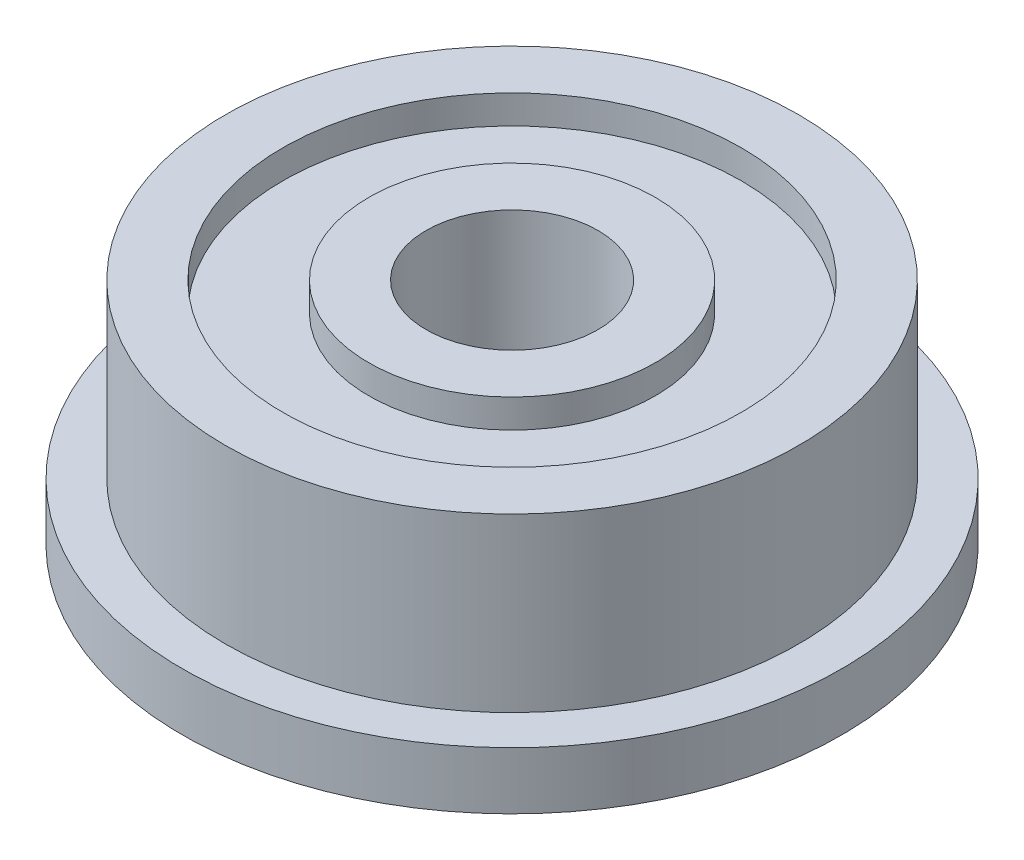
SolidWorks part; units mm, degrees
material "Chrome Stainless Steel"
ref_plane "Front Plane" through (0, 0, 0) normal (0, 0, 1) x (1, 0, 0)
ref_plane "Top Plane" through (0, 0, 0) normal (0, 1, 0) x (1, 0, 0)
ref_plane "Right Plane" through (0, 0, 0) normal (1, 0, 0) x (0, 0, -1)
sketch "Sketch1" plane through (0, 0, 0) normal (0, 0, 1) x (1, 0, 0)
  line L0 (0, -20.7975) -> (0, 26.0194) construction
  line L1 (1.5, 0) -> (1.5, 4)
  line L2 (1.5, 4) -> (2.5, 4)
  line L3 (5, 4) -> (5, 1)
  line L4 (5, 1) -> (5.75, 1)
  line L5 (5.75, 1) -> (5.75, 0)
  line L6 (5.75, 0) -> (4, 0)
  line L7 (4, 4) -> (5, 4)
  line L8 (2.5, 0) -> (1.5, 0)
  line L9 (2.5, 4) -> (2.5, 3.5)
  line L10 (2.5, 3.5) -> (4, 3.5)
  line L11 (4, 4) -> (4, 3.5)
  line L13 (2.5, 0) -> (2.5, 0.5)
  line L14 (2.5, 0.5) -> (4, 0.5)
  line L15 (4, 0) -> (4, 0.5)
  dimension "D1" = 3
  dimension "D2" = 10
  dimension "D3" = 11.5
  dimension "D4" = 1
  dimension "D5" = 4
  dimension "D6" = 1.5
  dimension "D7" = 0.5
revolve "Revolve1" add sketch "Sketch1" angle 360 about L0
